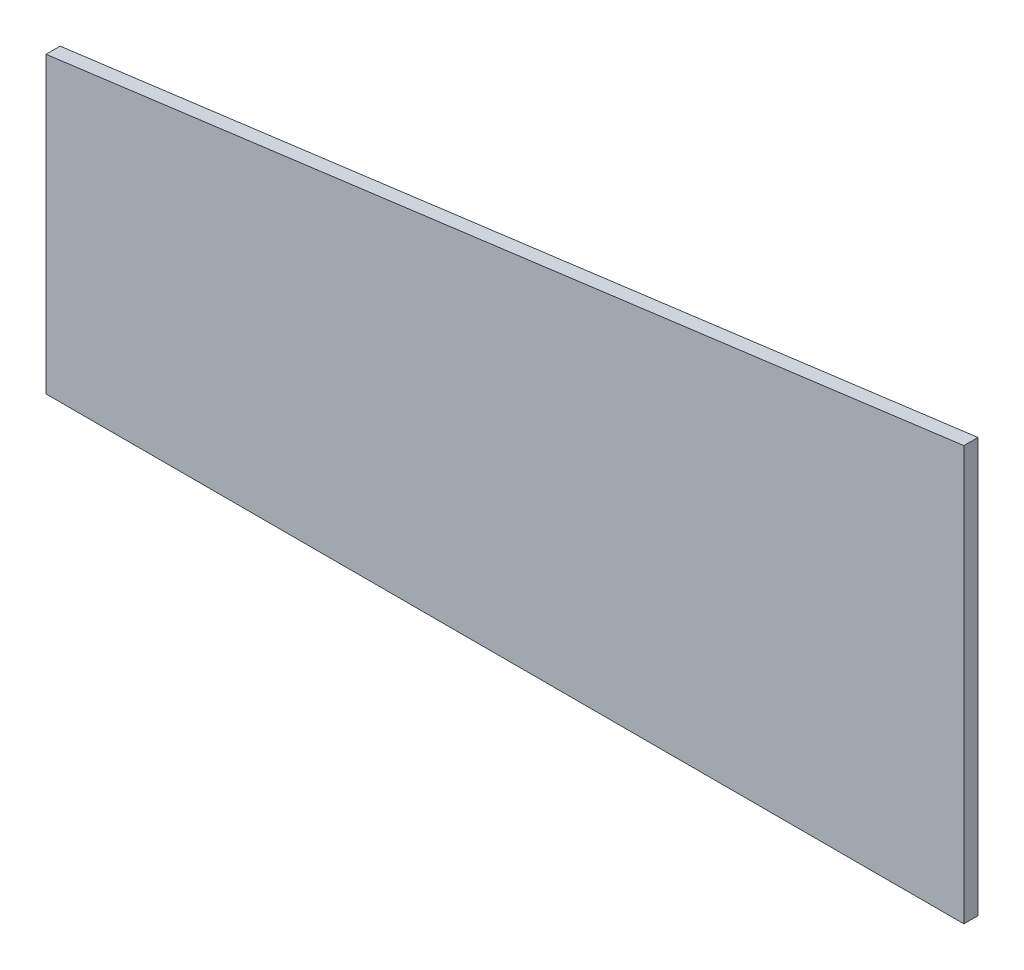
SolidWorks part; units mm, degrees
material "Pine"
ref_plane "Front Plane" through (0, 0, 0) normal (0, 0, 1) x (1, 0, 0)
ref_plane "Top Plane" through (0, 0, 0) normal (0, 1, 0) x (1, 0, 0)
ref_plane "Right Plane" through (0, 0, 0) normal (1, 0, 0) x (0, 0, -1)
sketch "Sketch1" plane through (0, 0, 0) normal (0, 0, 1) x (1, 0, 0)
  line L0 (1573.2125, -2392.3625) -> (-865.1875, -2392.3625) construction
  line L1 (-865.1875, -3611.5625) -> (1573.2125, -3611.5625) construction
  line L2 (-865.1875, -2392.3625) -> (-865.1875, -3611.5625) construction
  line L3 (1573.2125, -3611.5625) -> (1573.2125, -2392.3625) construction
  line L4 (373.0625, -3141.2661) -> (373.0625, -3611.5625) construction
  line L5 (-865.1875, -3611.5625) -> (-865.1875, -3214.6875) construction
  line L6 (373.0625, -3611.5625) -> (-865.1875, -3611.5625) construction
  line L7 (373.0625, -3141.2661) -> (373.0625, -3052.7725) construction
  line L8 (-865.1875, -3214.6875) -> (373.0625, -3052.7725) construction
  line L9 (373.0625, -2862.6589) -> (373.0625, -2392.3625) construction
  line L10 (-865.1875, -2392.3625) -> (-865.1875, -2789.2375) construction
  line L11 (373.0625, -2392.3625) -> (-865.1875, -2392.3625) construction
  line L12 (373.0625, -2862.6589) -> (373.0625, -2951.1525) construction
  line L13 (-865.1875, -2789.2375) -> (373.0625, -2951.1525) construction
  line L14 (-344.4875, -3046.4125) -> (-344.4875, -2957.5125) construction
  line L15 (173.0375, -3046.4125) -> (-344.4875, -3046.4125) construction
  line L16 (173.0375, -2957.5125) -> (173.0375, -3046.4125) construction
  line L17 (-344.4875, -2957.5125) -> (173.0375, -2957.5125) construction
  line L18 (-846.1375, -2791.7285) -> (-846.1375, -2392.3625) construction
  line L19 (-846.1375, -3611.5625) -> (-846.1375, -3212.1965) construction
  line L20 (-865.1875, -3046.4125) -> (-865.1875, -2957.5125) construction
  line L21 (-347.6625, -3046.4125) -> (-865.1875, -3046.4125) construction
  line L22 (-347.6625, -2957.5125) -> (-347.6625, -3046.4125) construction
  line L23 (-865.1875, -2957.5125) -> (-347.6625, -2957.5125) construction
  line L24 (-865.1875, -2954.3375) -> (-865.1875, -2865.4375) construction
  line L25 (-347.6625, -2954.3375) -> (-865.1875, -2954.3375) construction
  line L26 (-347.6625, -2865.4375) -> (-347.6625, -2954.3375) construction
  line L27 (-865.1875, -2865.4375) -> (-347.6625, -2865.4375) construction
  line L28 (-865.1875, -3138.4875) -> (-865.1875, -3049.5875) construction
  line L29 (-347.6625, -3138.4875) -> (-865.1875, -3138.4875) construction
  line L30 (-347.6625, -3049.5875) -> (-347.6625, -3138.4875) construction
  line L31 (-865.1875, -3049.5875) -> (-347.6625, -3049.5875) construction
  line L32 (376.2375, -3217.1617) -> (896.9375, -3217.1617) construction
  line L33 (896.9375, -3015.361) -> (376.2375, -3015.361) construction
  line L34 (376.2375, -3015.361) -> (376.2375, -3217.1617) construction
  line L35 (896.9375, -3217.1617) -> (896.9375, -3015.361) construction
  line L36 (915.9875, -3611.5625) -> (915.9875, -3224.2125) construction
  line L37 (395.2875, -3611.5625) -> (395.2875, -3224.2125) construction
  line L38 (376.2375, -3224.2125) -> (935.0375, -3224.2125) construction
  line L39 (935.0375, -3224.2125) -> (935.0375, -3611.5625) construction
  line L40 (373.0625, -3611.5625) -> (376.2375, -3224.2125) construction
  line L41 (935.0375, -3611.5625) -> (373.0625, -3611.5625) construction
  line L42 (900.1125, -2392.3625) -> (900.1125, -2916.2375) construction
  line L43 (1043.8597, -2916.2375) -> (1043.8597, -2392.3625) construction
  line L44 (900.1125, -2916.2375) -> (1043.8597, -2916.2375) construction
  line L45 (1043.8597, -2392.3625) -> (900.1125, -2392.3625) construction
  line L46 (1052.5125, -3611.5625) -> (1052.5125, -2411.4125) construction
  line L47 (1052.5125, -2411.4125) -> (1573.2125, -2411.4125) construction
  line L48 (1573.2125, -3611.5625) -> (1052.5125, -3611.5625) construction
  line L49 (1573.2125, -2411.4125) -> (1573.2125, -3611.5625) construction
  line L50 (896.9375, -2392.3625) -> (376.2375, -2392.3625) construction
  line L51 (376.2375, -3008.3125) -> (896.9375, -3008.3125) construction
  line L52 (896.9375, -3008.3125) -> (896.9375, -2392.3625) construction
  line L53 (376.2375, -2392.3625) -> (376.2375, -3008.3125) construction
  line L54 (-865.1875, -3611.5625) -> (-865.1875, -3214.6875)
  line L55 (-865.1875, -3214.6875) -> (373.0625, -3052.7725)
  line L56 (373.0625, -3052.7725) -> (373.0625, -3611.5625)
  line L57 (373.0625, -3611.5625) -> (-865.1875, -3611.5625)
extrude "Extrude1" add sketch "Sketch1" along normal blind 19.05
